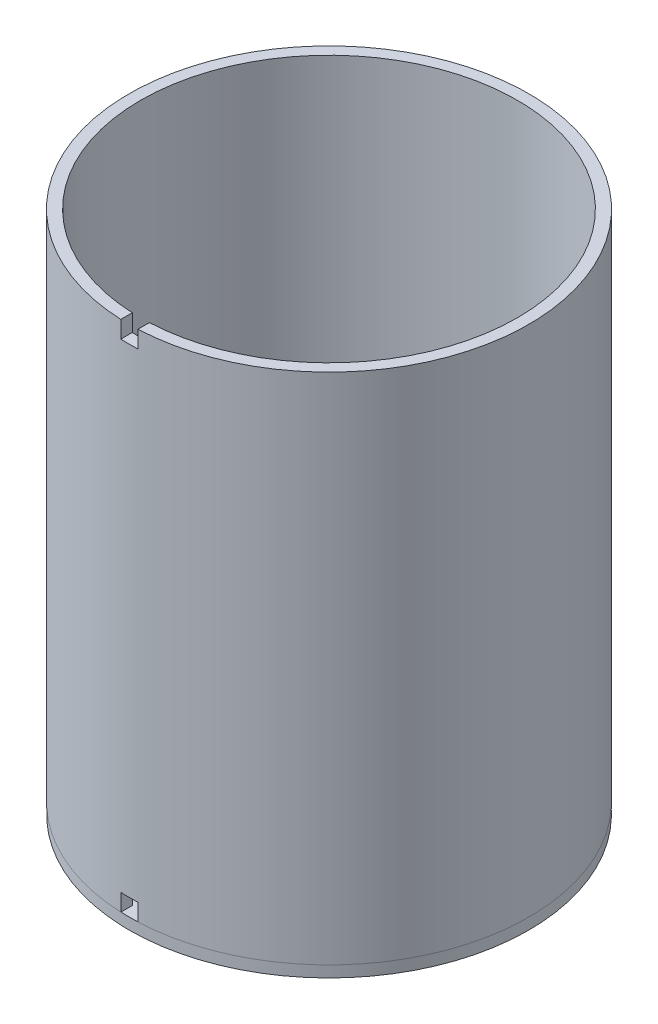
SolidWorks part; units mm, degrees
ref_plane "Front Plane" through (0, 0, 0) normal (0, 0, 1) x (1, 0, 0)
ref_plane "Top Plane" through (0, 0, 0) normal (0, 1, 0) x (1, 0, 0)
ref_plane "Right Plane" through (0, 0, 0) normal (1, 0, 0) x (0, 0, -1)
sketch "Sketch1" plane through (0, 0, 0) normal (0, 1, 0) x (1, 0, 0)
  circle A0 centre (0, 0) radius 88.9
  circle A1 centre (0, 0) radius 38.1
  dimension "D1" = 76.2
  dimension "D2" = 177.8
extrude "Boss-Extrude1" add sketch "Sketch1" along normal blind 5.08
sketch "Sketch2" plane through (0, 5.08, 0) normal (0, 1, 0) x (1, 0, 0)
  circle A0 centre (0, 0) radius 88.9699
  circle A1 centre (0, 0) radius 83.8899
  dimension "D1" = 5.08
extrude "Boss-Extrude2" add sketch "Sketch2" along normal blind 228.6
sketch "Sketch3" plane through (0, 0, 0) normal (0, 0, 1) x (1, 0, 0)
  line L0 (88.9699, 233.68) -> (-88.9699, 233.68) construction
  line L1 (-3.81, 233.68) -> (3.81, 233.68)
  line L2 (-3.81, 233.68) -> (-3.81, 226.06)
  line L3 (-3.81, 226.06) -> (3.81, 226.06)
  line L4 (3.81, 233.68) -> (3.81, 226.06)
  line L5 (0, 5.08) -> (0, 233.68) construction
  line L6 (-88.9699, 119.38) -> (88.9699, 119.38)
  line L7 (-88.9699, 233.68) -> (-88.9699, 5.08) construction
  line L8 (88.9699, 5.08) -> (88.9699, 233.68) construction
  line L9 (-88.9, 5.08) -> (88.9, 5.08) construction
  line L10 (0, 5.08) -> (0, 0) construction
  line L11 (-3.81, 5.08) -> (-3.81, 12.7)
  line L12 (-3.81, 5.08) -> (3.81, 5.08)
  line L13 (3.81, 5.08) -> (3.81, 12.7)
  line L14 (-3.81, 12.7) -> (3.81, 12.7)
  point P17 (0, 119.38)
  point P20 (0, 233.68)
  dimension "D1" = 7.62
  dimension "D2" = 7.62
extrude "Cut-Extrude1" cut sketch "Sketch3" along normal through all contours L4 L1 L2 L3 | L14 L11 L12 L13
